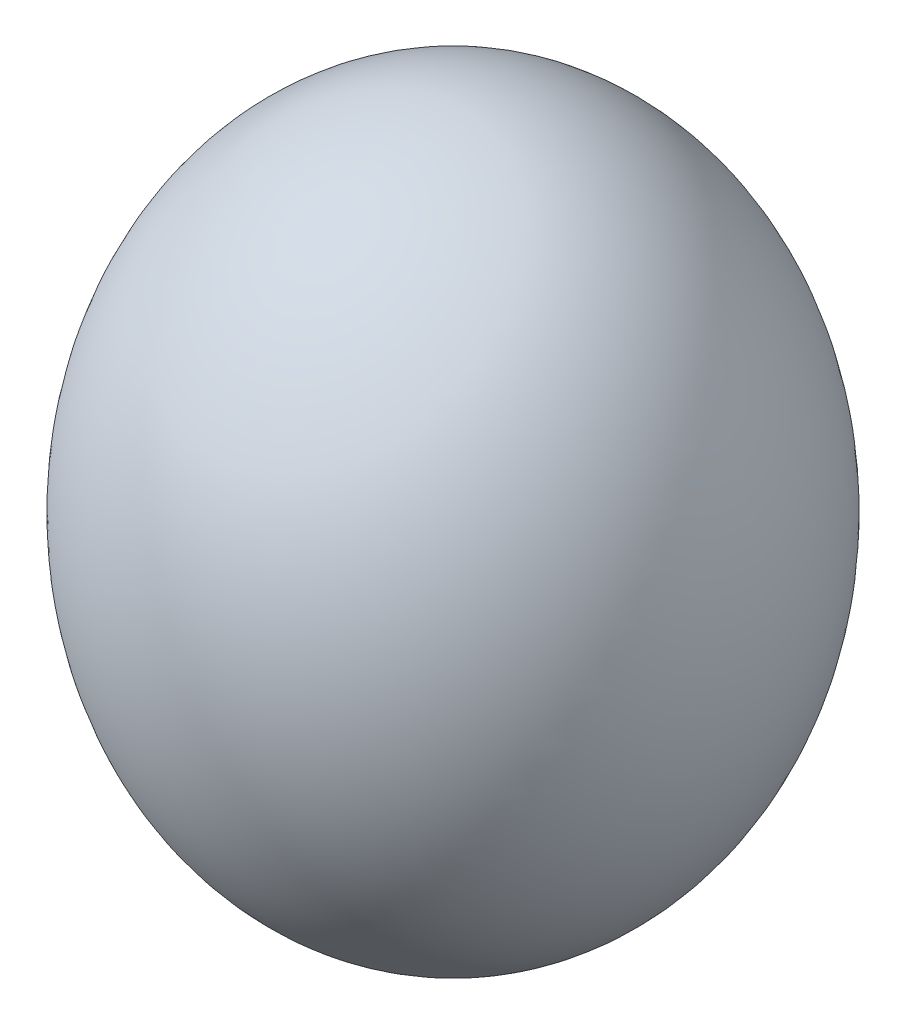
SolidWorks part; units mm, degrees
ref_plane "Alzado" through (0, 0, 0) normal (0, 0, 1) x (1, 0, 0)
ref_plane "Planta" through (0, 0, 0) normal (0, 1, 0) x (1, 0, 0)
ref_plane "Vista lateral" through (0, 0, 0) normal (1, 0, 0) x (0, 0, -1)
sketch "Croquis1" plane through (0, 0, 0) normal (0, 0, 1) x (1, 0, 0)
  line L0 (0, 0) -> (0, 65.6)
  ellipse E0 centre (0, 32.8) end of major axis (0, 65.6) minor radius 27 (0, 0) -> (0, 65.6) ccw
  dimension "D1" = 65.6
  dimension "D2" = 27
revolve "Revolución1" add sketch "Croquis1" angle 360 about L0
